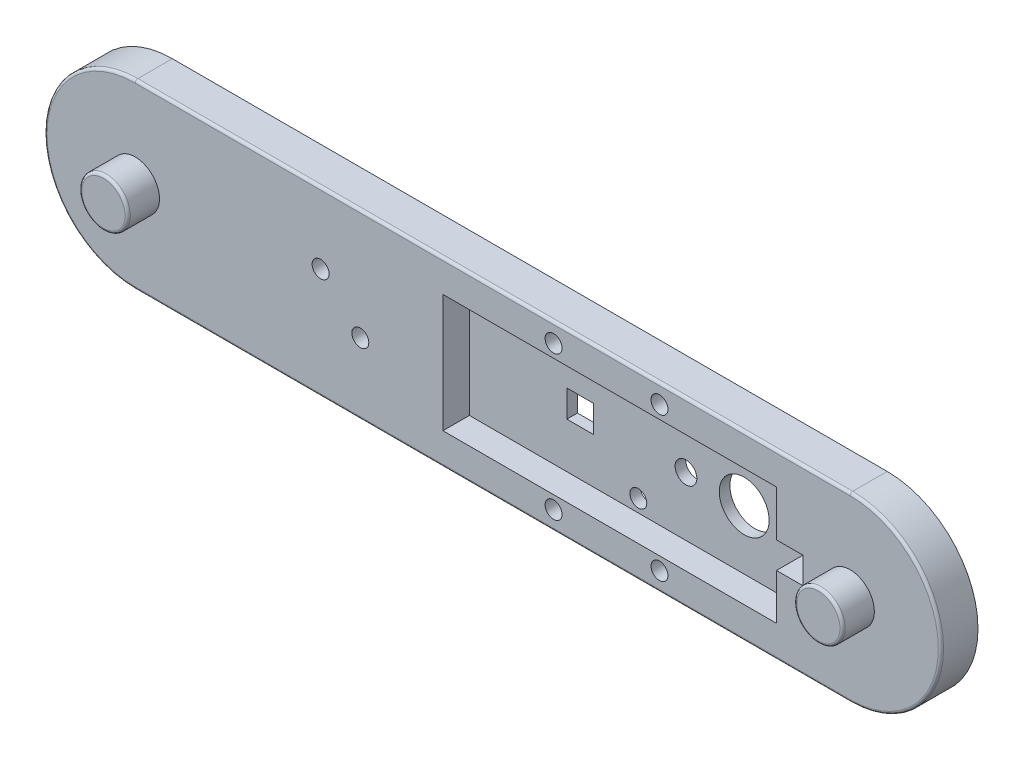
SolidWorks part; units mm, degrees
ref_plane "Front Plane" through (0, 0, 0) normal (0, 0, 1) x (1, 0, 0)
ref_plane "Top Plane" through (0, 0, 0) normal (0, 1, 0) x (1, 0, 0)
ref_plane "Right Plane" through (0, 0, 0) normal (1, 0, 0) x (0, 0, -1)
sketch "motor" plane through (0, 0, 0) normal (0, 0, 1) x (1, 0, 0)
  line L0 (-32.0436, 0) -> (38.1179, 0) construction
  line L1 (-1.825, 2) -> (1.825, 2)
  line L2 (-1.825, 2) -> (-1.825, -2)
  line L3 (-1.825, -2) -> (1.825, -2)
  line L4 (1.825, 2) -> (1.825, -2)
  line L5 (-1.825, 2) -> (1.825, -2) construction
  line L6 (-1.825, -2) -> (1.825, 2) construction
  line L7 (11.1, 2.5) -> (16.1, 2.5)
  line L8 (11.1, 2.5) -> (11.1, -2.5)
  line L9 (11.1, -2.5) -> (16.1, -2.5)
  line L10 (16.1, 2.5) -> (16.1, -2.5)
  line L11 (11.1, 2.5) -> (16.1, -2.5) construction
  line L12 (11.1, -2.5) -> (16.1, 2.5) construction
  line L13 (-51.9, 11.15) -> (11.1, 11.15)
  line L14 (-51.9, 11.15) -> (-51.9, -11.15)
  line L15 (-51.9, -11.15) -> (11.1, -11.15)
  line L16 (11.1, 11.15) -> (11.1, -11.15)
  line L17 (-51.9, 11.15) -> (11.1, -11.15) construction
  line L18 (-51.9, -11.15) -> (11.1, 11.15) construction
  line L19 (-52.9, 12.15) -> (12.1, 12.15)
  line L20 (12.1, 12.15) -> (12.1, -12.15)
  line L21 (-52.9, -12.15) -> (12.1, -12.15)
  line L22 (-52.9, 12.15) -> (-52.9, -12.15)
  line L23 (8.1, -3.5) -> (17.1, -3.5)
  line L24 (17.1, 3.5) -> (17.1, -3.5)
  line L25 (10.5, 3.5) -> (17.1, 3.5)
  line L28 (-33.5, 2.55) -> (-28.5, 2.55)
  line L29 (-33.5, 2.55) -> (-33.5, -2.55)
  line L30 (-33.5, -2.55) -> (-28.5, -2.55)
  line L31 (-28.5, 2.55) -> (-28.5, -2.55)
  line L32 (-33.5, 2.55) -> (-28.5, -2.55) construction
  line L33 (-33.5, -2.55) -> (-28.5, 2.55) construction
  circle A0 centre (0, 0) radius 2.7075
  circle A1 centre (-20, 8.75) radius 1.6
  circle A2 centre (-20, -8.75) radius 1.6
  circle A3 centre (-11, 0) radius 2.05
  point P0 (0, 0)
  point P8 (13.6, 0)
  point P13 (-20.4, 0)
  point P20 (11.1, 0)
  point P35 (-31, 0)
  dimension "D8" = 3.2
  dimension "D11" = 4.1
  dimension "D1" = 3.65
  dimension "D2" = 4
  dimension "D3" = 5
  dimension "D4" = 5
  dimension "D5" = 11.1
  dimension "D6" = 22.3
  dimension "D7" = 63
  dimension "D9" = 20
  dimension "D10" = 8.75
  dimension "D12" = 11
  dimension "D14" = 5
  dimension "D15" = 5.1
  dimension "D16" = 20
  dimension "D17" = 1
  dimension "D13" = 1
  dimension "D18" = 1
  dimension "D19" = 1
  dimension "D20" = 1
  dimension "D21" = 1
  dimension "D22" = 1
  dimension "D23" = 11
sketch "hole_distance" plane through (0, 0, 0) normal (0, 0, 1) x (1, 0, 0)
  circle A0 centre (-110, 0) radius 2.575
  circle A1 centre (25, 0) radius 2.575
  dimension "D1" = 5.15
  dimension "D2" = 5.15
  dimension "D3" = 135
  dimension "D4" = 25
sketch "Sketch6" plane through (0, 0, 0) normal (0, 0, 1) x (1, 0, 0)
  line L0 (-110, 17.15) -> (25, 17.15)
  line L1 (-110, -17.15) -> (25, -17.15)
  line L2 (-51.9, 11.15) -> (11.1, 11.15) construction
  line L3 (-33.5, -2.55) -> (-28.5, -2.55) construction
  line L4 (-33.5, 2.55) -> (-33.5, -2.55) construction
  line L5 (-33.5, 2.55) -> (-28.5, 2.55) construction
  line L6 (-28.5, 2.55) -> (-28.5, -2.55) construction
  line L7 (-33.5, -2.55) -> (-28.5, -2.55)
  line L8 (-33.5, 2.55) -> (-33.5, -2.55)
  line L9 (-33.5, 2.55) -> (-28.5, 2.55)
  line L10 (-28.5, 2.55) -> (-28.5, -2.55)
  line L11 (-51.9, 11.15) -> (-51.9, -11.15) construction
  line L12 (-51.9, -11.15) -> (11.1, -11.15) construction
  line L13 (11.1, 11.15) -> (11.1, -11.15) construction
  line L14 (11.1, -2.5) -> (16.1, -2.5) construction
  line L15 (16.1, 2.5) -> (16.1, -2.5) construction
  line L16 (11.1, 2.5) -> (16.1, 2.5) construction
  line L17 (-51.9, 11.15) -> (11.1, 11.15)
  line L18 (-51.9, 11.15) -> (-51.9, -11.15)
  line L19 (-51.9, -11.15) -> (11.1, -11.15)
  line L20 (11.1, 11.15) -> (11.1, -11.15)
  line L21 (11.1, -2.5) -> (16.1, -2.5)
  line L22 (16.1, 2.5) -> (16.1, -2.5)
  line L23 (11.1, 2.5) -> (16.1, 2.5)
  line L25 (-32.0436, 0) -> (38.1179, 0) construction
  line L26 (-32.0436, 0) -> (38.1179, 0) construction
  line L27 (-29.3546, 10.75) -> (-27.7091, 13.6) construction
  line L28 (-27.7091, 13.6) -> (-29.3546, 16.45) construction
  line L29 (-29.3546, 16.45) -> (-32.6454, 16.45) construction
  line L30 (-32.6454, 16.45) -> (-34.2909, 13.6) construction
  line L31 (-34.2909, 13.6) -> (-32.6454, 10.75) construction
  line L32 (-32.6454, 10.75) -> (-29.3546, 10.75) construction
  arc A0 (-110, -17.15) -> (-110, 17.15) centre (-110, 0) cw
  arc A1 (25, -17.15) -> (25, 17.15) centre (25, 0) ccw
  circle A2 centre (0, 0) radius 4.7075
  circle A3 centre (0, 0) radius 2.7075 construction
  circle A4 centre (-11, 0) radius 2.05 construction
  circle A5 centre (-20, 8.75) radius 1.6 construction
  circle A6 centre (-20, -8.75) radius 1.6 construction
  circle A7 centre (-11, 0) radius 2.05
  circle A8 centre (-20, 8.75) radius 1.6
  circle A9 centre (-20, -8.75) radius 1.6
  circle A10 centre (-110, 0) radius 2.575 construction
  circle A11 centre (25, 0) radius 2.575 construction
  circle A12 centre (-110, 0) radius 2.575
  circle A13 centre (25, 0) radius 2.575
  circle A14 centre (-31, 13.6) radius 1.6
  circle A15 centre (-11, 13.6) radius 1.6
  circle A16 centre (-11, -13.6) radius 1.6
  circle A17 centre (-31, -13.6) radius 1.6
  circle A18 centre (-31, 13.6) radius 2.85 construction
  dimension "D1" = 6
  dimension "D2" = 2
  dimension "D3" = 3.2
  dimension "D4" = 3.2
  dimension "D5" = 5.7
  dimension "D6" = 0.7
  dimension "D7" = 13.6
  dimension "D8" = 3.55
  dimension "D9" = 79
extrude "Boss-Extrude4" add sketch "Sketch6" along normal blind 2 contours L1 A1 L0 A0 A13 A12 L20 L23 L22 L21 L19 L18 L17 | L20 L17 L18 L19 A9 A8 A7 A2 L9 L10 L7 L8
sketch "Sketch7" plane through (0, 0, 2) normal (0, 0, 1) x (1, 0, 0)
  line L0 (-110, 17.15) -> (25, 17.15)
  line L1 (-110, -17.15) -> (25, -17.15)
  line L7 (-33.5, -2.55) -> (-28.5, -2.55)
  line L8 (-33.5, 2.55) -> (-33.5, -2.55)
  line L9 (-33.5, 2.55) -> (-28.5, 2.55)
  line L10 (-28.5, 2.55) -> (-28.5, -2.55)
  line L17 (-51.9, 11.15) -> (11.1, 11.15)
  line L18 (-51.9, 11.15) -> (-51.9, -11.15)
  line L19 (-51.9, -11.15) -> (11.1, -11.15)
  line L20 (11.1, 11.15) -> (11.1, -11.15)
  line L21 (11.1, -2.5) -> (16.1, -2.5)
  line L22 (16.1, 2.5) -> (16.1, -2.5)
  line L23 (11.1, 2.5) -> (16.1, 2.5)
  line L26 (-32.0436, 0) -> (38.1179, 0) construction
  line L27 (-29.3546, 10.75) -> (-27.7091, 13.6) construction
  line L28 (-27.7091, 13.6) -> (-29.3546, 16.45) construction
  line L29 (-29.3546, 16.45) -> (-32.6454, 16.45) construction
  line L30 (-32.6454, 16.45) -> (-34.2909, 13.6) construction
  line L31 (-34.2909, 13.6) -> (-32.6454, 10.75) construction
  line L32 (-32.6454, 10.75) -> (-29.3546, 10.75) construction
  arc A0 (-110, -17.15) -> (-110, 17.15) centre (-110, 0) cw
  arc A1 (25, -17.15) -> (25, 17.15) centre (25, 0) ccw
  circle A2 centre (0, 0) radius 4.7075
  circle A7 centre (-11, 0) radius 2.05
  circle A8 centre (-20, 8.75) radius 1.6
  circle A9 centre (-20, -8.75) radius 1.6
  circle A12 centre (-110, 0) radius 2.575
  circle A13 centre (25, 0) radius 2.575
  circle A14 centre (-31, 13.6) radius 1.6
  circle A15 centre (-11, 13.6) radius 1.6
  circle A16 centre (-11, -13.6) radius 1.6
  circle A17 centre (-31, -13.6) radius 1.6
  circle A18 centre (-31, 13.6) radius 2.85 construction
extrude "Boss-Extrude5" add sketch "Sketch7" along normal blind 5
sketch "Sketch8" plane through (0, 0, 7) normal (0, 0, 1) x (1, 0, 0)
  circle A0 centre (-75, 3.75) radius 1.6
  circle A1 centre (-67.5, -3.75) radius 1.6
  dimension "D1" = 3.2
  dimension "D2" = 3.2
  dimension "D3" = 3.75
  dimension "D4" = 35
  dimension "D5" = 7.5
  dimension "D6" = 7.5
extrude "midsection_holes" cut sketch "Sketch8" against normal through all
sketch "Sketch9" plane through (0, 0, 0) normal (0, 0, -1) x (-1, 0, 0)
  line L0 (110, 17.15) -> (-25, 17.15) construction
  line L1 (12.6454, 10.45) -> (14.2909, 13.3)
  line L2 (14.2909, 13.3) -> (12.6454, 16.15)
  line L3 (12.6454, 16.15) -> (9.3546, 16.15)
  line L4 (9.3546, 16.15) -> (7.7091, 13.3)
  line L5 (7.7091, 13.3) -> (9.3546, 10.45)
  line L6 (9.3546, 10.45) -> (12.6454, 10.45)
  line L7 (32.6454, 10.45) -> (34.2909, 13.3)
  line L8 (34.2909, 13.3) -> (32.6454, 16.15)
  line L9 (32.6454, 16.15) -> (29.3546, 16.15)
  line L10 (29.3546, 16.15) -> (27.7091, 13.3)
  line L11 (27.7091, 13.3) -> (29.3546, 10.45)
  line L12 (29.3546, 10.45) -> (32.6454, 10.45)
  line L13 (32.0436, 0) -> (-38.1179, 0) construction
  line L14 (32.0436, 0) -> (-38.1179, 0) construction
  line L15 (32.6454, -16.15) -> (29.3546, -16.15)
  line L16 (34.2909, -13.3) -> (32.6454, -16.15)
  line L17 (32.6454, -10.45) -> (34.2909, -13.3)
  line L18 (29.3546, -10.45) -> (32.6454, -10.45)
  line L19 (27.7091, -13.3) -> (29.3546, -10.45)
  line L20 (29.3546, -16.15) -> (27.7091, -13.3)
  line L21 (12.6454, -16.15) -> (9.3546, -16.15)
  line L22 (14.2909, -13.3) -> (12.6454, -16.15)
  line L23 (12.6454, -10.45) -> (14.2909, -13.3)
  line L24 (9.3546, -10.45) -> (12.6454, -10.45)
  line L25 (7.7091, -13.3) -> (9.3546, -10.45)
  line L26 (9.3546, -16.15) -> (7.7091, -13.3)
  circle A0 centre (11, 13.3) radius 2.85 construction
  circle A1 centre (31, 13.3) radius 2.85 construction
  dimension "D1" = 5.7
  dimension "D2" = 5.7
  dimension "D3" = 1
extrude "nutholes" [suppressed] cut sketch "Sketch9" against normal blind 2
sketch "Sketch12" plane through (0, 0, 7) normal (0, 0, 1) x (1, 0, 0)
  circle A0 centre (-110, 0) radius 4.575
  circle A1 centre (25, 0) radius 4.575
  circle A2 centre (-110, 0) radius 2.575 construction
  circle A3 centre (25, 0) radius 2.575 construction
  dimension "D1" = 2
  dimension "D2" = 2
extrude "Boss-Extrude6" add sketch "Sketch12" along normal blind 6
sketch "Sketch13" plane through (0, 0, 7) normal (0, 0, -1) x (-1, 0, 0)
  circle A0 centre (-25, 0) radius 2.575 construction
  circle A1 centre (110, 0) radius 2.575 construction
  circle A2 centre (-25, 0) radius 2.575
  circle A3 centre (110, 0) radius 2.575
extrude "Cut-Extrude4" cut sketch "Sketch13" against normal blind 4
fillet "Fillet1" radius 0.5 6 edges at (-105.425, 0, 13) (29.575, 0, 13) (-127.15, 0, 7) (-42.5, -17.15, 7) (42.15, 0, 7) (-42.5, 17.15, 7)
sketch "Sketch4" plane through (0, 0, 0) normal (0, 0, 1) x (1, 0, 0)
  line L0 (-1.825, 2) -> (-1.825, -2) construction
  line L1 (-36.3141, 11.2625) -> (14.3141, 11.2625)
  line L2 (-36.3141, 11.2625) -> (-36.3141, -11.2625)
  line L3 (-36.3141, -11.2625) -> (14.3141, -11.2625)
  line L4 (14.3141, 11.2625) -> (14.3141, -11.2625)
  line L5 (-36.3141, 11.2625) -> (14.3141, -11.2625) construction
  line L6 (-36.3141, -11.2625) -> (14.3141, 11.2625) construction
  line L7 (1.825, 2) -> (1.825, -2) construction
  line L8 (-1.825, 2) -> (-1.825, -2)
  line L9 (1.825, 2) -> (1.825, -2)
  line L10 (-33.5, 2.55) -> (-28.5, 2.55) construction
  line L11 (-28.5, 2.55) -> (-28.5, -2.55) construction
  line L12 (-33.5, -2.55) -> (-28.5, -2.55) construction
  line L13 (-33.5, 2.55) -> (-33.5, -2.55) construction
  line L14 (-33.5, 2.55) -> (-28.5, 2.55)
  line L15 (-28.5, 2.55) -> (-28.5, -2.55)
  line L16 (-33.5, -2.55) -> (-28.5, -2.55)
  line L17 (-33.5, 2.55) -> (-33.5, -2.55)
  circle A0 centre (-20, 8.75) radius 1.6 construction
  circle A1 centre (-11, 0) radius 2.05 construction
  circle A2 centre (-20, -8.75) radius 1.6 construction
  circle A3 centre (0, 0) radius 2.7075 construction
  circle A4 centre (-20, 8.75) radius 1.6
  circle A5 centre (-11, 0) radius 2.05
  circle A6 centre (-20, -8.75) radius 1.6
  circle A7 centre (0, 0) radius 2.7075
  point P0 (-11, 0)
extrude "Boss-Extrude3" [suppressed] add sketch "Sketch4" along normal blind 0.6 contours L4 L1 L2 L3 A7 A6 A5 A4 | L8 A7 | L9 A7
sketch "Sketch2" plane through (0, 0, 0) normal (0, 0, 1) x (1, 0, 0)
  line L0 (-52.9, 12.15) -> (12.1, 12.15) construction
  line L1 (12.1, 12.15) -> (12.1, -12.15) construction
  line L2 (-52.9, -12.15) -> (12.1, -12.15) construction
  line L3 (-52.9, 12.15) -> (-52.9, -12.15) construction
  line L4 (-52.9, 12.15) -> (12.1, 12.15)
  line L5 (12.1, 12.15) -> (12.1, -12.15)
  line L6 (-52.9, -12.15) -> (12.1, -12.15)
  line L7 (-52.9, 12.15) -> (-52.9, -12.15)
  line L8 (10.5, 3.5) -> (17.1, 3.5) construction
  line L9 (17.1, 3.5) -> (17.1, -3.5) construction
  line L10 (8.1, -3.5) -> (17.1, -3.5) construction
  line L11 (10.5, 3.5) -> (17.1, 3.5)
  line L12 (17.1, 3.5) -> (17.1, -3.5)
  line L13 (8.1, -3.5) -> (17.1, -3.5)
  line L14 (-33.5, 2.55) -> (-28.5, 2.55) construction
  line L15 (-28.5, 2.55) -> (-28.5, -2.55) construction
  line L16 (-33.5, -2.55) -> (-28.5, -2.55) construction
  line L17 (-33.5, 2.55) -> (-33.5, -2.55) construction
  line L18 (-1.825, 2) -> (-1.825, -2) construction
  line L19 (1.825, 2) -> (1.825, -2) construction
  line L20 (-33.5, 2.55) -> (-28.5, 2.55)
  line L21 (-28.5, 2.55) -> (-28.5, -2.55)
  line L22 (-33.5, -2.55) -> (-28.5, -2.55)
  line L23 (-33.5, 2.55) -> (-33.5, -2.55)
  line L24 (-1.825, 2) -> (-1.825, -2)
  line L25 (1.825, 2) -> (1.825, -2)
  circle A0 centre (-20, 8.75) radius 1.6 construction
  circle A1 centre (-11, 0) radius 2.05 construction
  circle A2 centre (-20, -8.75) radius 1.6 construction
  circle A3 centre (0, 0) radius 2.7075 construction
  circle A4 centre (-20, 8.75) radius 1.6
  circle A5 centre (-11, 0) radius 2.05
  circle A6 centre (-20, -8.75) radius 1.6
  circle A7 centre (0, 0) radius 2.7075
extrude "Boss-Extrude1" [suppressed] add sketch "Sketch2" along normal blind 0.6
sketch "Sketch3" [suppressed] plane through (0, 0, 0.6) normal (0, 0, 1) x (1, 0, 0)
  line L0 (-52.9, 12.15) -> (12.1, 12.15) construction
  line L1 (12.1, 12.15) -> (12.1, -12.15) construction
  line L2 (-52.9, -12.15) -> (12.1, -12.15) construction
  line L3 (-52.9, 12.15) -> (-52.9, -12.15) construction
  line L4 (-52.9, 12.15) -> (12.1, 12.15)
  line L5 (12.1, 12.15) -> (12.1, -12.15)
  line L6 (-52.9, -12.15) -> (12.1, -12.15)
  line L7 (-52.9, 12.15) -> (-52.9, -12.15)
  line L8 (11.1, 11.15) -> (11.1, -11.15) construction
  line L9 (-51.9, -11.15) -> (11.1, -11.15) construction
  line L10 (-51.9, 11.15) -> (-51.9, -11.15) construction
  line L11 (-51.9, 11.15) -> (11.1, 11.15) construction
  line L12 (11.1, 11.15) -> (11.1, -11.15)
  line L13 (-51.9, -11.15) -> (11.1, -11.15)
  line L14 (-51.9, 11.15) -> (-51.9, -11.15)
  line L15 (-51.9, 11.15) -> (11.1, 11.15)
  line L16 (11.1, 2.5) -> (16.1, 2.5) construction
  line L17 (16.1, 2.5) -> (16.1, -2.5) construction
  line L18 (11.1, -2.5) -> (16.1, -2.5) construction
  line L19 (11.1, 2.5) -> (11.1, -2.5) construction
  line L20 (11.1, 2.5) -> (16.1, 2.5)
  line L21 (16.1, 2.5) -> (16.1, -2.5)
  line L22 (11.1, -2.5) -> (16.1, -2.5)
  line L23 (11.1, 2.5) -> (11.1, -2.5)
  line L24 (10.5, 3.5) -> (17.1, 3.5) construction
  line L25 (17.1, 3.5) -> (17.1, -3.5) construction
  line L26 (8.1, -3.5) -> (17.1, -3.5) construction
  line L27 (10.5, 3.5) -> (17.1, 3.5)
  line L28 (17.1, 3.5) -> (17.1, -3.5)
  line L29 (8.1, -3.5) -> (17.1, -3.5)
  line M1 (12.1, 3.5) -> (12.1, 12.15)
  line M2 (12.1, 12.15) -> (-52.9, 12.15)
  line M3 (-52.9, 12.15) -> (-52.9, -12.15)
  line M4 (-52.9, -12.15) -> (12.1, -12.15)
  line M5 (12.1, -12.15) -> (12.1, -3.5)
  line M6 (12.1, -3.5) -> (17.1, -3.5)
  line M7 (17.1, -3.5) -> (17.1, 3.5)
  line M8 (17.1, 3.5) -> (12.1, 3.5)
extrude "Boss-Extrude2" [suppressed] add sketch "Sketch3" along normal blind 5 separate body contours L29 L12 L13 L14 L15 L27 M1 M2 M3 M4 M5 | L22 L5 L20 L21 M6 M7 M8 | L27 L12 L20 L5 | L12 L29 L5 L22
equation "\"D19@motor\"=\"D17@motor\""
equation "\"D13@motor\"=\"D17@motor\""
equation "\"D18@motor\"=\"D17@motor\""
equation "\"D20@motor\"=\"D17@motor\""
equation "\"D21@motor\"=\"D17@motor\""
equation "\"D22@motor\"=\"D17@motor\""
equation "\"D2@hole_distance\"=5.15"
equation "\"D2@Sketch9\"=\"D1@Sketch9\""
